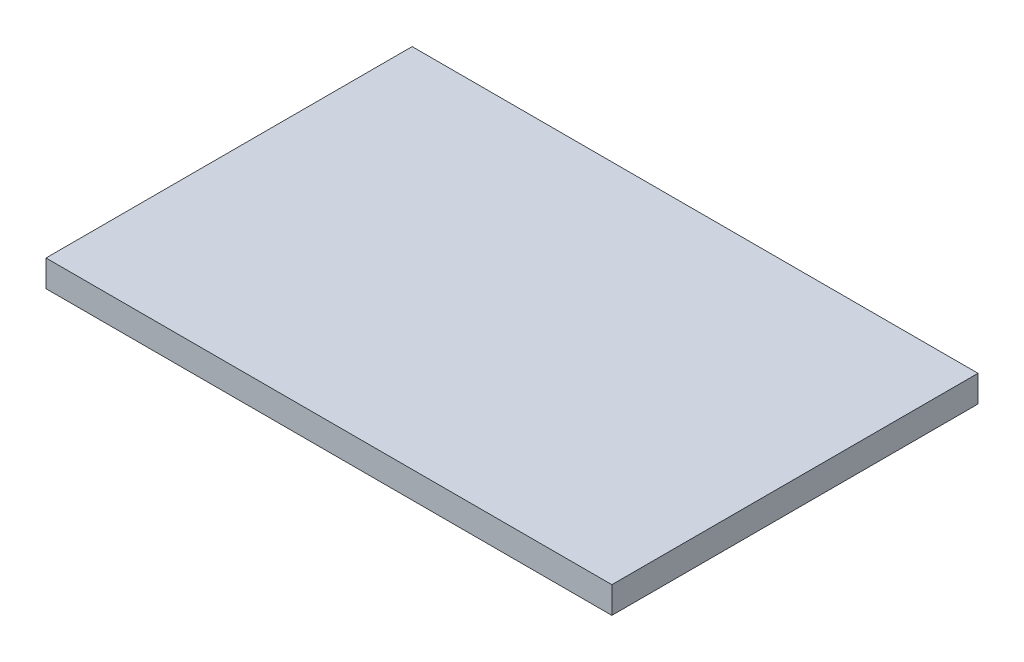
SolidWorks part; units mm, degrees
material "玻璃"
ref_plane "前视基准面" through (0, 0, 0) normal (0, 0, 1) x (1, 0, 0)
ref_plane "上视基准面" through (0, 0, 0) normal (0, 1, 0) x (1, 0, 0)
ref_plane "右视基准面" through (0, 0, 0) normal (1, 0, 0) x (0, 0, -1)
other "Configuration Table"
sketch "草图1" plane through (0, 0, 0) normal (0, 1, 0) x (1, 0, 0)
  line L1 (0, 0) -> (85, 0)
  line L2 (0, 0) -> (0, -55)
  line L3 (0, -55) -> (85, -55)
  line L4 (85, 0) -> (85, -55)
  dimension "D1" = 85
  dimension "D2" = 55
extrude "凸台-拉伸1" add sketch "草图1" along normal blind 4
